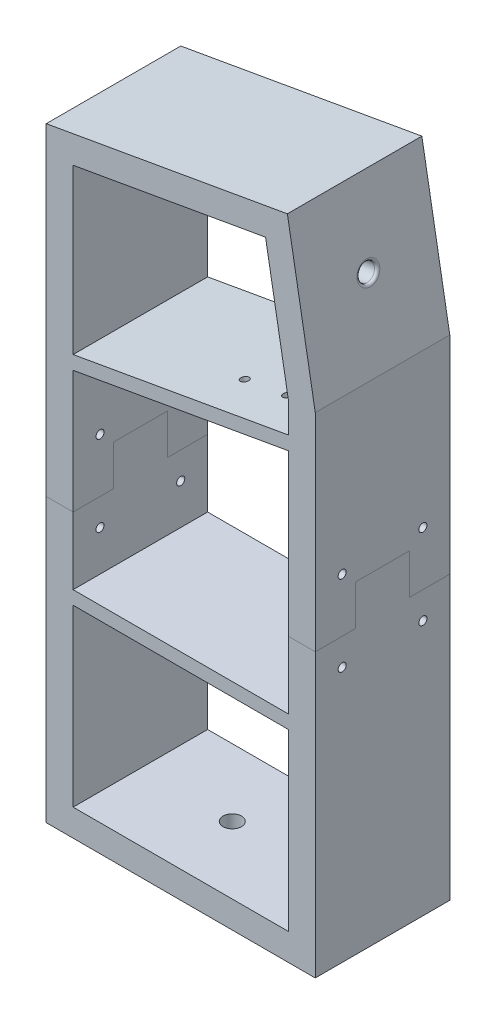
SolidWorks part; units mm, degrees
ref_plane "Front Plane" through (0, 0, 0) normal (0, 0, 1) x (1, 0, 0)
ref_plane "Top Plane" through (0, 0, 0) normal (0, 1, 0) x (1, 0, 0)
ref_plane "Right Plane" through (0, 0, 0) normal (1, 0, 0) x (0, 0, -1)
sketch "Sketch2" plane through (0, 0, 0) normal (0, 0, 1) x (1, 0, 0)
  line L6 (-50, 225.01) -> (-50, 0)
  line L8 (-50, 0) -> (50, 0)
  line L10 (-40, 216.619) -> (-40, 10)
  line L11 (-40, 10) -> (40, 10)
  line L12 (50, 0) -> (50, 182.01)
  line L13 (50, 182.01) -> (39.6312, 240.8144)
  line L14 (50, 182.01) -> (50, 266.0824) construction
  line L15 (39.6312, 240.8144) -> (-50, 225.01)
  line L16 (40, 10) -> (40, 181.1351)
  line L17 (40, 181.1351) -> (31.5196, 229.2298)
  line L18 (31.5196, 229.2298) -> (-40, 216.619)
  dimension "D1" = 182.01
  dimension "D2" = 100
  dimension "D3" = 10
  dimension "D4" = 225.01
  dimension "D6" = 10
extrude "Boss-Extrude1" add sketch "Sketch2" along normal blind 50
sketch "Sketch4" plane through (79.6179, 14.0388, 0) normal (0.9848, 0.1736, 0) x (0, 0, -1)
  line L0 (-25, 170.5625) -> (-25, 200.891) construction
  line L1 (-50, 170.5625) -> (0, 170.5625) construction
  line L2 (-50, 230.274) -> (0, 230.274) construction
  circle A0 centre (-25, 200.891) radius 3.2
  dimension "D1" = 6.4
  dimension "D2" = 29.383
extrude "Cut-Extrude1" cut sketch "Sketch4" against normal blind 10
sketch "Sketch7" plane through (0, 0, 50) normal (0, 0, 1) x (1, 0, 0)
  line L1 (40, 10) -> (40, 181.1351) construction
  line L5 (40, 169.7996) -> (40, 164.7224)
  line L7 (-40, 150.6163) -> (-40, 155.6934)
  line L10 (40, 169.7996) -> (-40, 155.6934)
  line L11 (-40, 150.6163) -> (40, 164.7224)
  line L12 (-40, 216.619) -> (-40, 10) construction
  line L13 (31.5196, 229.2298) -> (-40, 216.619) construction
  dimension "D1" = 60
  dimension "D3" = 5
extrude "Boss-Extrude2" add sketch "Sketch7" against normal blind 50
sketch "Sketch8" plane through (-50, 0, 0) normal (-1, 0, 0) x (0, 0, 1)
  line L0 (50, 225.01) -> (0, 225.01) construction
  line L1 (50, 225.01) -> (50, 0) construction
  line L3 (0, 225.01) -> (0, 0) construction
  line L4 (0, 204.1639) -> (50, 204.1639) construction
  circle A0 centre (25, 204.1639) radius 5
  dimension "D1" = 10
  dimension "D2" = 20.8461
extrude "Cut-Extrude3" cut sketch "Sketch8" against normal blind 10
sketch "Sketch9" plane through (128.3774, 180.3057, 0) normal (-0.1736, 0.9848, 0) x (-0.9848, -0.1736, 0)
  line L0 (76.8907, 25) -> (104.9692, 25) construction
  line L3 (104.9692, 34.6) -> (120.9692, 34.6) construction
  line L5 (76.8907, 50) -> (76.8907, 0) construction
  line L6 (104.9692, 25) -> (104.9692, 34.6) construction
  line L7 (104.9692, 25) -> (104.9692, 15.4) construction
  line L8 (120.9692, 34.6) -> (120.9692, 15.4) construction
  line L10 (120.9692, 15.4) -> (104.9692, 15.4) construction
  circle A0 centre (104.9692, 15.4) radius 1.485
  circle A1 centre (104.9692, 34.6) radius 1.485
  circle A2 centre (120.9692, 34.6) radius 1.485
  circle A3 centre (120.9692, 15.4) radius 1.485
  dimension "D1" = 28.0785
  dimension "D2" = 2.97
  dimension "D3" = 19.2
  dimension "D4" = 16
extrude "Cut-Extrude4" cut sketch "Sketch9" along normal up to next contours A3
sketch "Sketch10" plane through (0, 10, 0) normal (0, 1, 0) x (1, 0, 0)
  line L0 (50, -25) -> (24.131, -25) construction
  line L1 (-30.869, -50) -> (-30.869, 0) construction
  line L2 (50, -50) -> (50, 0) construction
  line L3 (-30, -25) -> (-5.8513, -25) construction
  circle A0 centre (-5.8513, -25) radius 3.425
  circle A1 centre (24.131, -25) radius 3.425
  dimension "D1" = 6.85
  dimension "D2" = 6.85
  dimension "D3" = 25.0177
  dimension "D4" = 55
extrude "Cut-Extrude5" cut sketch "Sketch10" against normal blind 10
sketch "Sketch11" plane through (0, 0, 50) normal (0, 0, 1) x (1, 0, 0)
  line L0 (-40, 75) -> (40, 75)
  line L3 (40, 75) -> (40, 80)
  line L4 (40, 80) -> (-40, 80)
  line L5 (-40, 80) -> (-40, 75)
  line L6 (-40, 150.6163) -> (-40, 10) construction
  line L7 (40, 10) -> (40, 164.7224) construction
  dimension "D1" = 5
  dimension "D2" = 75
extrude "Boss-Extrude3" add sketch "Sketch11" against normal blind 50
fillet "Fillet1" radius 1 1 edges at (44.1778, 215.0292, 25)
sketch "Sketch13" plane through (-50, 0, 0) normal (-1, 0, 0) x (0, 0, 1)
  line L0 (0, 0) -> (0, 105) construction
  line L1 (50, 105) -> (50, 95) construction
  line L2 (0, 105) -> (15, 105)
  line L3 (15, 105) -> (15, 120)
  line L4 (15, 120) -> (35, 120)
  line L5 (35, 120) -> (35, 105)
  line L6 (35, 105) -> (50, 105)
  line L7 (50, 225.01) -> (50, 0) construction
  line L8 (50, 0) -> (0, 0) construction
  line L9 (0, 105) -> (0, 96.1035) construction
  line L10 (50, 95) -> (40, 95) construction
  line L11 (50, 105) -> (50, 125) construction
  line L12 (50, 125) -> (40, 125) construction
  line L13 (25, 120) -> (25, -15) construction
  circle A0 centre (40, 125) radius 1.5
  circle A1 centre (40, 95) radius 1.5
  circle A4 centre (10, 95) radius 1.5
  circle A5 centre (10, 125) radius 1.5
  point P25 (0, 0)
  dimension "D6" = 3
  dimension "D7" = 3
  dimension "D1" = 15
  dimension "D2" = 35
  dimension "D3" = 15
  dimension "D4" = 120
  dimension "D5" = 105
extrude "Cut-Extrude6" cut sketch "Sketch13" against normal through all contours A4 | A5 | A0 | A1
sketch "Sketch14" plane through (-50, 0, 0) normal (-1, 0, 0) x (0, 0, 1)
  line L0 (50, 0) -> (50, 105) construction
  line L1 (50, 225.01) -> (50, 0) construction
  line L2 (50, 105) -> (35, 105)
  line L3 (35, 105) -> (35, 120)
  line L4 (35, 120) -> (15, 120)
  line L5 (15, 120) -> (15, 105)
  line L6 (15, 105) -> (0, 105)
  line L7 (0, 225.01) -> (0, 0) construction
  line L8 (50, 0) -> (0, 0) construction
  dimension "D1" = 15
  dimension "D2" = 35
  dimension "D3" = 15
  dimension "D4" = 120
  dimension "D5" = 105
split "Split1" trim tools "Sketch14" bodies to split 113 resulting bodies 114 115
